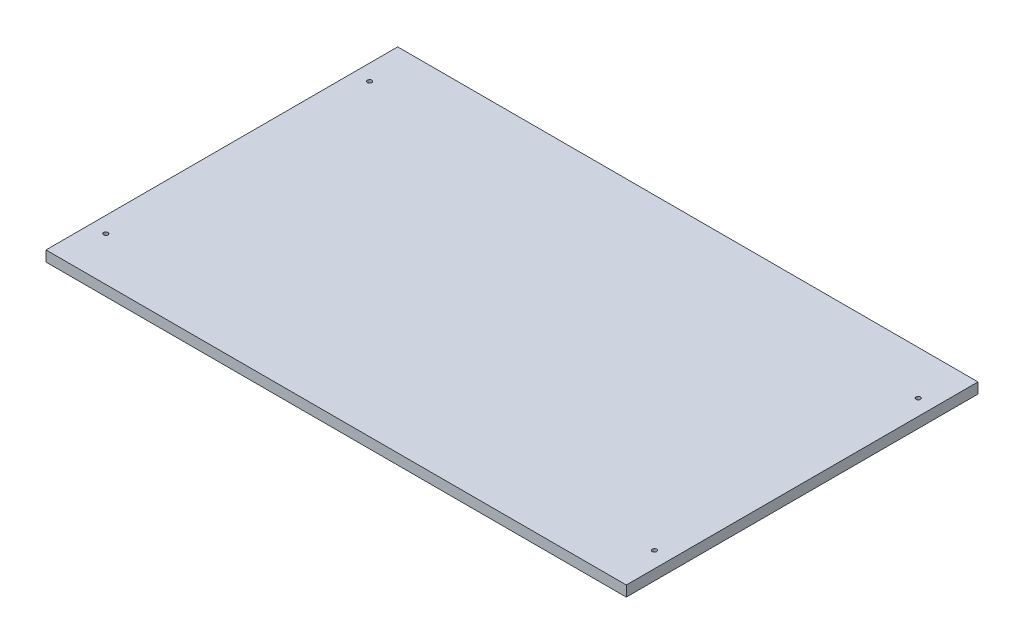
SolidWorks part; units mm, degrees
material "PBT General Purpose"
ref_plane "Front Plane" through (0, 0, 0) normal (0, 0, 1) x (1, 0, 0)
ref_plane "Top Plane" through (0, 0, 0) normal (0, 1, 0) x (1, 0, 0)
ref_plane "Right Plane" through (0, 0, 0) normal (1, 0, 0) x (0, 0, -1)
sketch "Sketch1" plane through (0, 0, 0) normal (0, 1, 0) x (1, 0, 0)
  line L1 (0, 0) -> (330, 0)
  line L2 (0, 0) -> (0, 200)
  line L3 (0, 200) -> (330, 200)
  line L4 (330, 0) -> (330, 200)
  dimension "D1" = 330
extrude "Boss-Extrude1" add sketch "Sketch1" along normal blind 6
sketch "Sketch4" plane through (0, 0, 0) normal (0, -1, 0) x (1, 0, 0)
  line L2 (0, -200) -> (0, 0) construction
  line L4 (330, -200) -> (0, -200) construction
  line L5 (0, 0) -> (330, 0) construction
  line L6 (330, 0) -> (330, -200) construction
  circle A0 centre (9, -175) radius 1.25
  circle A1 centre (9, -25) radius 1.25
  circle A2 centre (321, -175) radius 1.25
  circle A3 centre (321, -25) radius 1.25
  dimension "D1" = 25
  dimension "D2" = 9
  dimension "D3" = 9
  dimension "D4" = 25
  dimension "D5" = 9
  dimension "D6" = 25
  dimension "D7" = 9
  dimension "D8" = 25
extrude "Cut-Extrude1" cut sketch "Sketch4" against normal through all
